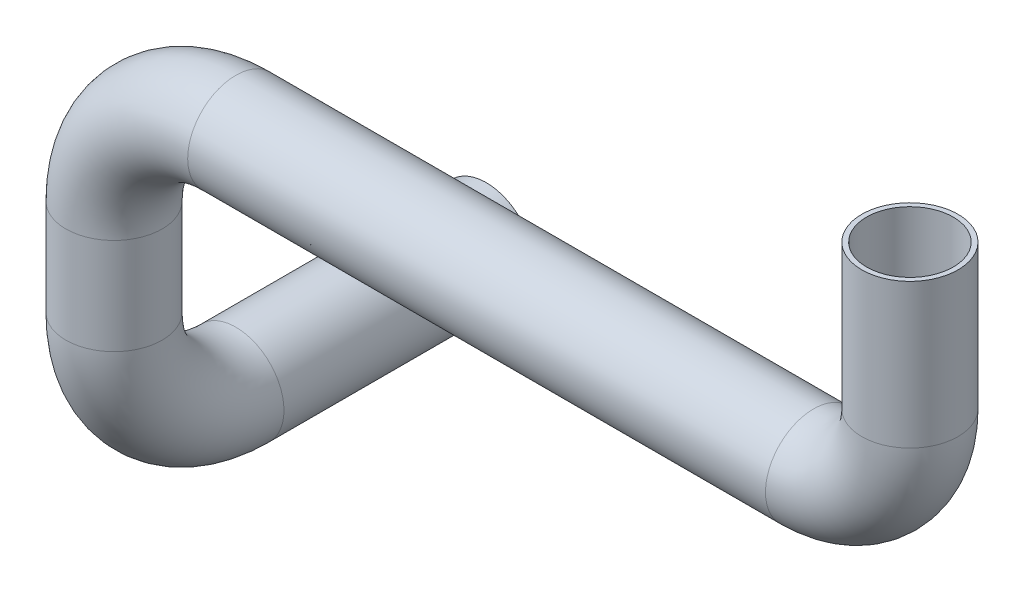
SolidWorks part; units mm, degrees
material "Beryllium Copper, UNS C17000"
ref_plane "Front Plane" through (0, 0, 0) normal (0, 0, 1) x (1, 0, 0)
ref_plane "Top Plane" through (0, 0, 0) normal (0, 1, 0) x (1, 0, 0)
ref_plane "Right Plane" through (0, 0, 0) normal (1, 0, 0) x (0, 0, -1)
sketch "Sketch1" plane through (0, 0, 0) normal (0, 0, 1) x (1, 0, 0)
  line L0 (40, 25) -> (40, 10)
  line L1 (30, 0) -> (-30, 0)
  line L2 (-42.65, -12.65) -> (-42.65, -22.65)
  arc A0 (40, 10) -> (30, 0) centre (30, 10) cw
  arc A1 (-30, 0) -> (-42.65, -12.65) centre (-30, -12.65) ccw
  dimension "D1" = 10
  dimension "D2" = 12.65
  dimension "D3" = 10
  dimension "D4" = 60
  dimension "D5" = 15
ref_plane "Plane1" through (0, 25, 0) normal (0, 1, 0) x (1, 0, 0)
sketch "Sketch2" plane through (0, 25, 0) normal (0, 1, 0) x (1, 0, 0)
  circle A0 centre (40, 0) radius 5
  dimension "D1" = 10
ref_plane "Plane2" through (-42.65, 0, 0) normal (1, 0, 0) x (0, 0, -1)
sketch "Sketch4" plane through (-42.65, 0, 0) normal (1, 0, 0) x (0, 0, -1)
  line L0 (0, -12.65) -> (0, -22.65)
  line L1 (12.65, -35.3) -> (38.65, -35.3)
  arc A0 (0, -22.65) -> (12.65, -35.3) centre (12.65, -22.65) ccw
  dimension "D1" = 12.65
  dimension "D2" = 26
  dimension "D3" = 10
sweep "Sweep1" add profiles "Sketch2" path "Sketch1"
sketch "Sketch5" plane through (0, -22.65, 0) normal (0, -1, 0) x (1, 0, 0)
  circle A1 centre (-42.65, 0) radius 5
  circle A2 centre (-42.65, 0) radius 5
  dimension "D1" = 0
sweep "Sweep2" add profiles "Sketch5" path "Sketch4"
shell "Shell1" thickness 0.5
